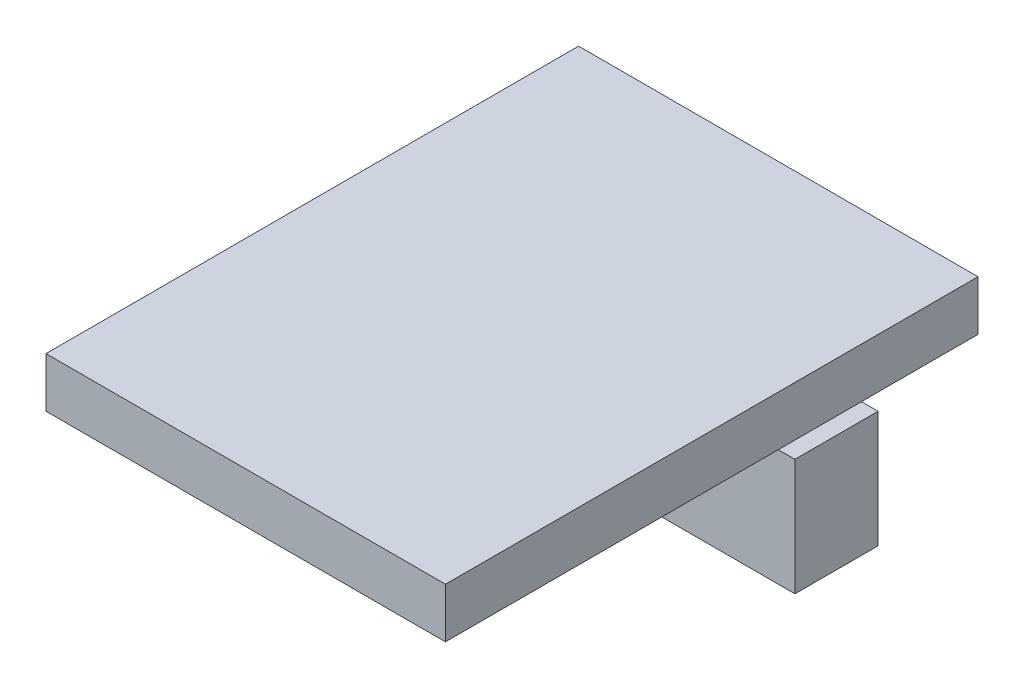
SolidWorks part; units mm, degrees
ref_plane "Front Plane" through (0, 0, 0) normal (0, 0, 1) x (1, 0, 0)
ref_plane "Top Plane" through (0, 0, 0) normal (0, 1, 0) x (1, 0, 0)
ref_plane "Right Plane" through (0, 0, 0) normal (1, 0, 0) x (0, 0, -1)
sketch "Sketch1" plane through (0, 0, 0) normal (0, 1, 0) x (1, 0, 0)
  line L1 (-22.3304, 17.6348) -> (1.6696, 17.6348)
  line L2 (-22.3304, 17.6348) -> (-22.3304, -14.3652)
  line L3 (-22.3304, -14.3652) -> (1.6696, -14.3652)
  line L4 (1.6696, 17.6348) -> (1.6696, -14.3652)
  dimension "D1" = 24
  dimension "D2" = 32
extrude "Boss-Extrude1" add sketch "Sketch1" along normal blind 3
sketch "Sketch2" plane through (0, 3, 0) normal (0, 1, 0) x (1, 0, 0)
  line L0 (1.6696, 17.6348) -> (-22.3304, 17.6348) construction
  line L1 (-15.3304, 12.6348) -> (-13.8304, 12.6348)
  line L2 (-15.3304, 12.6348) -> (-15.3304, 9.6348)
  line L3 (-15.3304, 9.6348) -> (-13.8304, 9.6348)
  line L4 (-13.8304, 12.6348) -> (-13.8304, 9.6348)
  line L5 (-6.8304, 12.6348) -> (-6.8304, 9.6348)
  line L6 (-6.8304, 12.6348) -> (-5.3304, 12.6348)
  line L7 (-5.3304, 12.6348) -> (-5.3304, 9.6348)
  line L8 (-6.8304, 9.6348) -> (-5.3304, 9.6348)
  line L9 (-22.3304, 17.6348) -> (-22.3304, -14.3652) construction
  line L10 (1.6696, -14.3652) -> (1.6696, 17.6348) construction
  dimension "D1" = 5
  dimension "D2" = 1.5
  dimension "D3" = 3
  dimension "D5" = 7
  dimension "D6" = 7
  dimension "D4" = 2
extrude "Boss-Extrude5" add sketch "Sketch2" against normal blind 6
sketch "Sketch3" plane through (0, -3, 0) normal (0, -1, 0) x (1, 0, 0)
  line L0 (1.6696, -17.6348) -> (-22.3304, -17.6348) construction
  line L1 (-20.3304, -8.6348) -> (-0.3304, -8.6348)
  line L2 (-20.3304, -8.6348) -> (-20.3304, -13.6348)
  line L3 (-20.3304, -13.6348) -> (-0.3304, -13.6348)
  line L4 (-0.3304, -8.6348) -> (-0.3304, -13.6348)
  line L5 (-22.3304, -17.6348) -> (-22.3304, 14.3652) construction
  dimension "D1" = 20
  dimension "D2" = 5
  dimension "D3" = 4
  dimension "D4" = 2
extrude "Boss-Extrude6" add sketch "Sketch3" along normal blind 7
